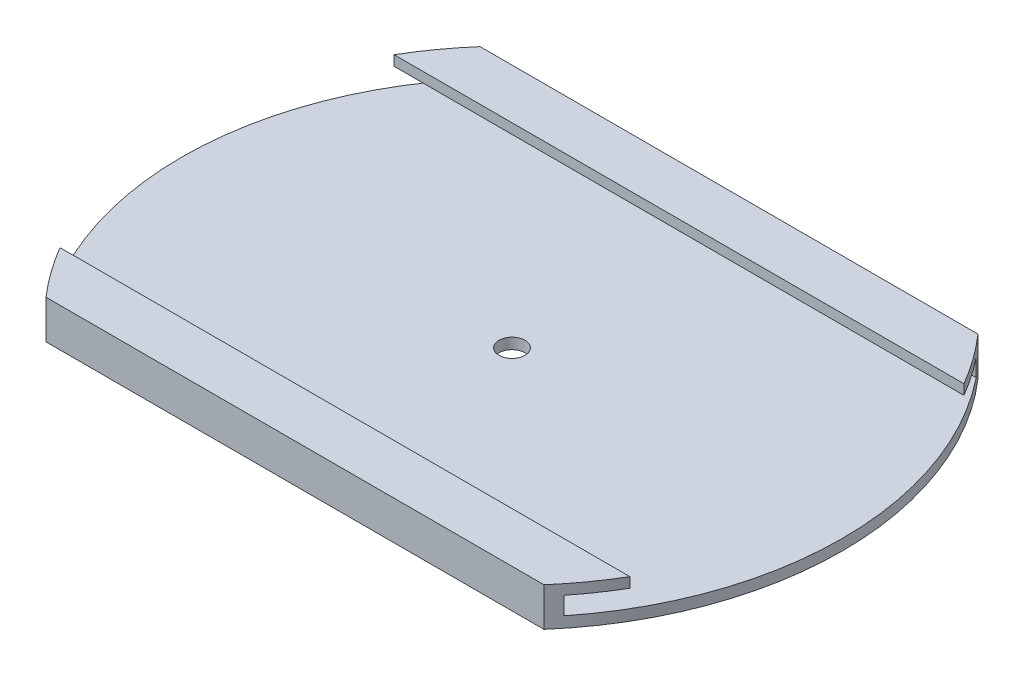
SolidWorks part; units mm, degrees
ref_plane "Front Plane" through (0, 0, 0) normal (0, 0, 1) x (1, 0, 0)
ref_plane "Top Plane" through (0, 0, 0) normal (0, 1, 0) x (1, 0, 0)
ref_plane "Right Plane" through (0, 0, 0) normal (1, 0, 0) x (0, 0, -1)
sketch "Sketch3" plane through (0, 0, 0) normal (0, 1, 0) x (1, 0, 0)
  line L1 (-57.3, 49.95) -> (57.3, 49.95)
  line L3 (-57.3, -49.95) -> (57.3, -49.95)
  line L5 (-57.3, 49.95) -> (57.3, -49.95) construction
  line L6 (-57.3, -49.95) -> (57.3, 49.95) construction
  arc A0 (-57.3, 49.95) -> (-57.3, -49.95) centre (0, 0) ccw
  arc A1 (57.3, 49.95) -> (57.3, -49.95) centre (0, 0) cw
  point P0 (0, 0)
  dimension "D1" = 114.6
  dimension "D2" = 99.9
extrude "Boss-Extrude1" add sketch "Sketch3" along normal blind 8.9
sketch "Sketch4" plane through (0, 0, 0) normal (1, 0, 0) x (0, 0, -1)
  line L0 (-49.95, 8.9) -> (-49.95, 0) construction
  line L1 (-47.45, 6.5801) -> (47.45, 6.5801)
  line L2 (-47.45, 6.5801) -> (-47.45, 2.5)
  line L3 (-47.45, 2.5) -> (47.45, 2.5)
  line L4 (47.45, 6.5801) -> (47.45, 2.5)
  line L5 (49.95, 8.9) -> (49.95, 0) construction
  line L6 (-49.95, 0) -> (49.95, 0) construction
  dimension "D1" = 2.5
  dimension "D2" = 2.5
  dimension "D3" = 2.5
extrude "Cut-Extrude1" cut sketch "Sketch4" against normal through all both and the other way through all
sketch "Sketch7" plane through (0, 0, 0) normal (1, 0, 0) x (0, 0, -1)
  line L0 (49.95, 8.9) -> (-49.95, 8.9) construction
  line L1 (-38.45, 8.9) -> (38.45, 8.9)
  line L2 (-38.45, 8.9) -> (-38.45, 6.5801)
  line L3 (-38.45, 6.5801) -> (38.45, 6.5801)
  line L4 (38.45, 8.9) -> (38.45, 6.5801)
  line L5 (-47.45, 6.5801) -> (47.45, 6.5801) construction
  line L6 (-49.95, 8.9) -> (-49.95, 0) construction
  line L7 (49.95, 8.9) -> (49.95, 0) construction
  dimension "D1" = 11.5
  dimension "D2" = 11.5
extrude "Cut-Extrude2" cut sketch "Sketch7" against normal through all both and the other way through all
sketch "Sketch8" plane through (0, 2.5, 0) normal (0, 1, 0) x (1, 0, 0)
  circle A0 centre (0, 0) radius 3
  dimension "D1" = 6
extrude "Cut-Extrude3" cut sketch "Sketch8" against normal through all both and the other way through all
